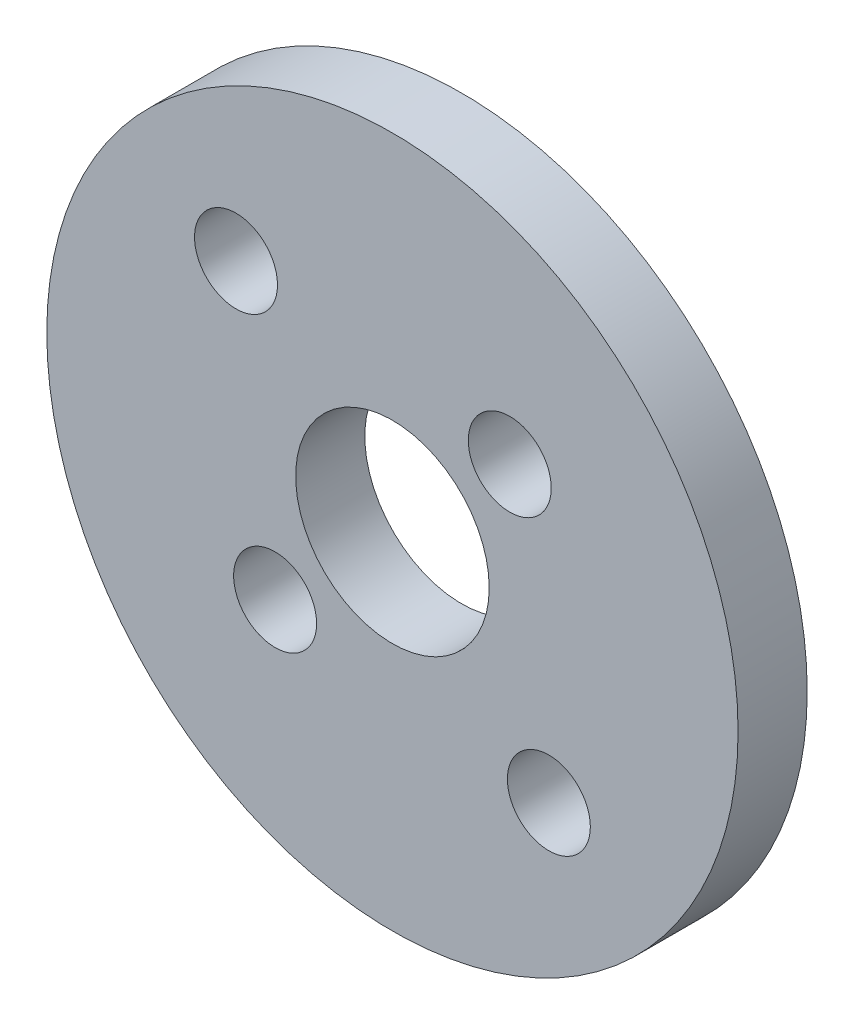
SolidWorks part; units mm, degrees
ref_plane "Front Plane" through (0, 0, 0) normal (0, 0, 1) x (1, 0, 0)
ref_plane "Top Plane" through (0, 0, 0) normal (0, 1, 0) x (1, 0, 0)
ref_plane "Right Plane" through (0, 0, 0) normal (1, 0, 0) x (0, 0, -1)
sketch "Sketch1" plane through (0, 0, 0) normal (0, 0, 1) x (1, 0, 0)
  circle A17 centre (5.6569, -155.6569) radius 1.5
  circle A18 centre (4.2426, -145.7574) radius 1.5
  circle A19 centre (-5.6569, -144.3431) radius 1.5
  circle A20 centre (-4.2426, -154.2426) radius 1.5
  circle A28 centre (0, -150) radius 3.5
  circle A35 centre (0, -150) radius 12.5
  dimension "D2" = 3
  dimension "D3" = 7
  dimension "D1" = 25
extrude "Boss-Extrude1" add sketch "Sketch1" along normal blind 2.5
